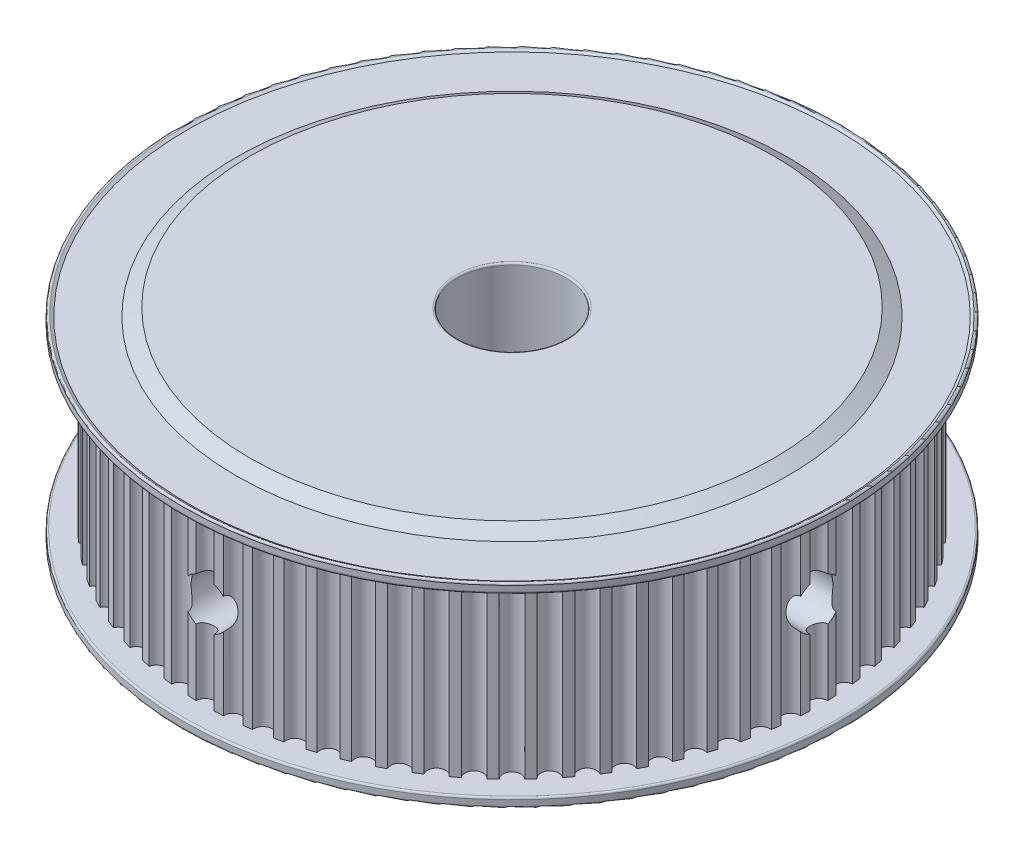
SolidWorks part; units mm, degrees
material "1060 Alloy"
ref_plane "Front Plane" through (0, 0, 0) normal (0, 0, 1) x (1, 0, 0)
ref_plane "Top Plane" through (0, 0, 0) normal (0, 1, 0) x (1, 0, 0)
ref_plane "Right Plane" through (0, 0, 0) normal (1, 0, 0) x (0, 0, -1)
sketch "Sketch1" plane through (0, 0, 0) normal (0, 0, 1) x (1, 0, 0)
  line L0 (0, 0) -> (0, 23) construction
  line L1 (0, 0) -> (0, 1.75)
  line L2 (0, 1.75) -> (36.5, 1.75)
  line L3 (36.5, 1.75) -> (36.5, 0.55)
  line L4 (36.5, 0.55) -> (35.8938, 0.9)
  line L5 (35.8938, 0.9) -> (30.5588, 0.9)
  line L6 (30.5588, 0.9) -> (29, 0)
  line L7 (29, 0) -> (0, 0)
  dimension "D1" = 23
  dimension "D3" = 36.5
  dimension "D4" = 29
  dimension "D5" = 150
  dimension "D6" = 150
  dimension "D7" = 1.75
  dimension "D8" = 1.2
  dimension "D9" = 0.85
revolve "Revolve1" add sketch "Sketch1" angle 360 about L0
fillet "Fillet1" radius 0.2 2 edges at (0, 0.55, -36.5) (0, 1.75, -36.5)
sketch "Sketch2" plane through (0, 1.75, 0) normal (0, 1, 0) x (1, 0, 0)
  arc A0 (1.9659, 33.9431) -> (0.9999, 33.9853) centre (0, 0) ccw
  circle A1 centre (0, 0) radius 33 construction
  arc A2 (-0.9999, 33.9853) -> (0.9999, 33.9853) centre (0, 34) ccw
  arc A3 (4.9168, 33.6426) -> (3.9581, 33.7688) centre (0, 0) ccw
  arc A4 (1.9659, 33.9431) -> (3.9581, 33.7688) centre (2.9633, 33.8706) ccw
  arc A5 (7.8302, 33.0861) -> (6.8862, 33.2954) centre (0, 0) ccw
  arc A6 (4.9168, 33.6426) -> (6.8862, 33.2954) centre (5.904, 33.4835) ccw
  arc A7 (10.6841, 32.2777) -> (9.7619, 32.5685) centre (0, 0) ccw
  arc A8 (7.8302, 33.0861) -> (9.7619, 32.5685) centre (8.7998, 32.8415) ccw
  arc A9 (13.4566, 31.2237) -> (12.5632, 31.5937) centre (0, 0) ccw
  arc A10 (10.6841, 32.2777) -> (12.5632, 31.5937) centre (11.6287, 31.9495) ccw
  arc A11 (16.1267, 29.9321) -> (15.269, 30.3786) centre (0, 0) ccw
  arc A12 (13.4566, 31.2237) -> (15.269, 30.3786) centre (14.369, 30.8145) ccw
  arc A13 (18.6741, 28.4126) -> (17.8586, 28.9322) centre (0, 0) ccw
  arc A14 (16.1267, 29.9321) -> (17.8586, 28.9322) centre (17, 29.4449) ccw
  arc A15 (21.0794, 26.677) -> (20.3122, 27.2656) centre (0, 0) ccw
  arc A16 (18.6741, 28.4126) -> (20.3122, 27.2656) centre (19.5016, 27.8512) ccw
  arc A17 (23.3242, 24.7383) -> (22.6113, 25.3915) centre (0, 0) ccw
  arc A18 (21.0794, 26.677) -> (22.6113, 25.3915) centre (21.8548, 26.0455) ccw
  arc A19 (25.3915, 22.6113) -> (24.7383, 23.3242) centre (0, 0) ccw
  arc A20 (23.3242, 24.7383) -> (24.7383, 23.3242) centre (24.0416, 24.0416) ccw
  arc A21 (27.2656, 20.3122) -> (26.677, 21.0794) centre (0, 0) ccw
  arc A22 (25.3915, 22.6113) -> (26.677, 21.0794) centre (26.0455, 21.8548) ccw
  arc A23 (28.9322, 17.8586) -> (28.4126, 18.6741) centre (0, 0) ccw
  arc A24 (27.2656, 20.3122) -> (28.4126, 18.6741) centre (27.8512, 19.5016) ccw
  arc A25 (30.3786, 15.269) -> (29.9321, 16.1267) centre (0, 0) ccw
  arc A26 (28.9322, 17.8586) -> (29.9321, 16.1267) centre (29.4449, 17) ccw
  arc A27 (31.5937, 12.5632) -> (31.2237, 13.4566) centre (0, 0) ccw
  arc A28 (30.3786, 15.269) -> (31.2237, 13.4566) centre (30.8145, 14.369) ccw
  arc A29 (32.5685, 9.7619) -> (32.2777, 10.6841) centre (0, 0) ccw
  arc A30 (31.5937, 12.5632) -> (32.2777, 10.6841) centre (31.9495, 11.6287) ccw
  arc A31 (33.2954, 6.8862) -> (33.0861, 7.8302) centre (0, 0) ccw
  arc A32 (32.5685, 9.7619) -> (33.0861, 7.8302) centre (32.8415, 8.7998) ccw
  arc A33 (33.7688, 3.9581) -> (33.6426, 4.9168) centre (0, 0) ccw
  arc A34 (33.2954, 6.8862) -> (33.6426, 4.9168) centre (33.4835, 5.904) ccw
  arc A35 (33.9853, 0.9999) -> (33.9431, 1.9659) centre (0, 0) ccw
  arc A36 (33.7688, 3.9581) -> (33.9431, 1.9659) centre (33.8706, 2.9633) ccw
  arc A37 (33.9431, -1.9659) -> (33.9853, -0.9999) centre (0, 0) ccw
  arc A38 (33.9853, 0.9999) -> (33.9853, -0.9999) centre (34, 0) ccw
  arc A39 (33.6426, -4.9168) -> (33.7688, -3.9581) centre (0, 0) ccw
  arc A40 (33.9431, -1.9659) -> (33.7688, -3.9581) centre (33.8706, -2.9633) ccw
  arc A41 (33.0861, -7.8302) -> (33.2954, -6.8862) centre (0, 0) ccw
  arc A42 (33.6426, -4.9168) -> (33.2954, -6.8862) centre (33.4835, -5.904) ccw
  arc A43 (32.2777, -10.6841) -> (32.5685, -9.7619) centre (0, 0) ccw
  arc A44 (33.0861, -7.8302) -> (32.5685, -9.7619) centre (32.8415, -8.7998) ccw
  arc A45 (31.2237, -13.4566) -> (31.5937, -12.5632) centre (0, 0) ccw
  arc A46 (32.2777, -10.6841) -> (31.5937, -12.5632) centre (31.9495, -11.6287) ccw
  arc A47 (29.9321, -16.1267) -> (30.3786, -15.269) centre (0, 0) ccw
  arc A48 (31.2237, -13.4566) -> (30.3786, -15.269) centre (30.8145, -14.369) ccw
  arc A49 (28.4126, -18.6741) -> (28.9322, -17.8586) centre (0, 0) ccw
  arc A50 (29.9321, -16.1267) -> (28.9322, -17.8586) centre (29.4449, -17) ccw
  arc A51 (26.677, -21.0794) -> (27.2656, -20.3122) centre (0, 0) ccw
  arc A52 (28.4126, -18.6741) -> (27.2656, -20.3122) centre (27.8512, -19.5016) ccw
  arc A53 (24.7383, -23.3242) -> (25.3915, -22.6113) centre (0, 0) ccw
  arc A54 (26.677, -21.0794) -> (25.3915, -22.6113) centre (26.0455, -21.8548) ccw
  arc A55 (22.6113, -25.3915) -> (23.3242, -24.7383) centre (0, 0) ccw
  arc A56 (24.7383, -23.3242) -> (23.3242, -24.7383) centre (24.0416, -24.0416) ccw
  arc A57 (20.3122, -27.2656) -> (21.0794, -26.677) centre (0, 0) ccw
  arc A58 (22.6113, -25.3915) -> (21.0794, -26.677) centre (21.8548, -26.0455) ccw
  arc A59 (17.8586, -28.9322) -> (18.6741, -28.4126) centre (0, 0) ccw
  arc A60 (20.3122, -27.2656) -> (18.6741, -28.4126) centre (19.5016, -27.8512) ccw
  arc A61 (15.269, -30.3786) -> (16.1267, -29.9321) centre (0, 0) ccw
  arc A62 (17.8586, -28.9322) -> (16.1267, -29.9321) centre (17, -29.4449) ccw
  arc A63 (12.5632, -31.5937) -> (13.4566, -31.2237) centre (0, 0) ccw
  arc A64 (15.269, -30.3786) -> (13.4566, -31.2237) centre (14.369, -30.8145) ccw
  arc A65 (9.7619, -32.5685) -> (10.6841, -32.2777) centre (0, 0) ccw
  arc A66 (12.5632, -31.5937) -> (10.6841, -32.2777) centre (11.6287, -31.9495) ccw
  arc A67 (6.8862, -33.2954) -> (7.8302, -33.0861) centre (0, 0) ccw
  arc A68 (9.7619, -32.5685) -> (7.8302, -33.0861) centre (8.7998, -32.8415) ccw
  arc A69 (3.9581, -33.7688) -> (4.9168, -33.6426) centre (0, 0) ccw
  arc A70 (6.8862, -33.2954) -> (4.9168, -33.6426) centre (5.904, -33.4835) ccw
  arc A71 (0.9999, -33.9853) -> (1.9659, -33.9431) centre (0, 0) ccw
  arc A72 (3.9581, -33.7688) -> (1.9659, -33.9431) centre (2.9633, -33.8706) ccw
  arc A73 (-1.9659, -33.9431) -> (-0.9999, -33.9853) centre (0, 0) ccw
  arc A74 (0.9999, -33.9853) -> (-0.9999, -33.9853) centre (0, -34) ccw
  arc A75 (-4.9168, -33.6426) -> (-3.9581, -33.7688) centre (0, 0) ccw
  arc A76 (-1.9659, -33.9431) -> (-3.9581, -33.7688) centre (-2.9633, -33.8706) ccw
  arc A77 (-7.8302, -33.0861) -> (-6.8862, -33.2954) centre (0, 0) ccw
  arc A78 (-4.9168, -33.6426) -> (-6.8862, -33.2954) centre (-5.904, -33.4835) ccw
  arc A79 (-10.6841, -32.2777) -> (-9.7619, -32.5685) centre (0, 0) ccw
  arc A80 (-7.8302, -33.0861) -> (-9.7619, -32.5685) centre (-8.7998, -32.8415) ccw
  arc A81 (-13.4566, -31.2237) -> (-12.5632, -31.5937) centre (0, 0) ccw
  arc A82 (-10.6841, -32.2777) -> (-12.5632, -31.5937) centre (-11.6287, -31.9495) ccw
  arc A83 (-16.1267, -29.9321) -> (-15.269, -30.3786) centre (0, 0) ccw
  arc A84 (-13.4566, -31.2237) -> (-15.269, -30.3786) centre (-14.369, -30.8145) ccw
  arc A85 (-18.6741, -28.4126) -> (-17.8586, -28.9322) centre (0, 0) ccw
  arc A86 (-16.1267, -29.9321) -> (-17.8586, -28.9322) centre (-17, -29.4449) ccw
  arc A87 (-21.0794, -26.677) -> (-20.3122, -27.2656) centre (0, 0) ccw
  arc A88 (-18.6741, -28.4126) -> (-20.3122, -27.2656) centre (-19.5016, -27.8512) ccw
  arc A89 (-23.3242, -24.7383) -> (-22.6113, -25.3915) centre (0, 0) ccw
  arc A90 (-21.0794, -26.677) -> (-22.6113, -25.3915) centre (-21.8548, -26.0455) ccw
  arc A91 (-25.3915, -22.6113) -> (-24.7383, -23.3242) centre (0, 0) ccw
  arc A92 (-23.3242, -24.7383) -> (-24.7383, -23.3242) centre (-24.0416, -24.0416) ccw
  arc A93 (-27.2656, -20.3122) -> (-26.677, -21.0794) centre (0, 0) ccw
  arc A94 (-25.3915, -22.6113) -> (-26.677, -21.0794) centre (-26.0455, -21.8548) ccw
  arc A95 (-28.9322, -17.8586) -> (-28.4126, -18.6741) centre (0, 0) ccw
  arc A96 (-27.2656, -20.3122) -> (-28.4126, -18.6741) centre (-27.8512, -19.5016) ccw
  arc A97 (-30.3786, -15.269) -> (-29.9321, -16.1267) centre (0, 0) ccw
  arc A98 (-28.9322, -17.8586) -> (-29.9321, -16.1267) centre (-29.4449, -17) ccw
  arc A99 (-31.5937, -12.5632) -> (-31.2237, -13.4566) centre (0, 0) ccw
  arc A100 (-30.3786, -15.269) -> (-31.2237, -13.4566) centre (-30.8145, -14.369) ccw
  arc A101 (-32.5685, -9.7619) -> (-32.2777, -10.6841) centre (0, 0) ccw
  arc A102 (-31.5937, -12.5632) -> (-32.2777, -10.6841) centre (-31.9495, -11.6287) ccw
  arc A103 (-33.2954, -6.8862) -> (-33.0861, -7.8302) centre (0, 0) ccw
  arc A104 (-32.5685, -9.7619) -> (-33.0861, -7.8302) centre (-32.8415, -8.7998) ccw
  arc A105 (-33.7688, -3.9581) -> (-33.6426, -4.9168) centre (0, 0) ccw
  arc A106 (-33.2954, -6.8862) -> (-33.6426, -4.9168) centre (-33.4835, -5.904) ccw
  arc A107 (-33.9853, -0.9999) -> (-33.9431, -1.9659) centre (0, 0) ccw
  arc A108 (-33.7688, -3.9581) -> (-33.9431, -1.9659) centre (-33.8706, -2.9633) ccw
  arc A109 (-33.9431, 1.9659) -> (-33.9853, 0.9999) centre (0, 0) ccw
  arc A110 (-33.9853, -0.9999) -> (-33.9853, 0.9999) centre (-34, 0) ccw
  arc A111 (-33.6426, 4.9168) -> (-33.7688, 3.9581) centre (0, 0) ccw
  arc A112 (-33.9431, 1.9659) -> (-33.7688, 3.9581) centre (-33.8706, 2.9633) ccw
  arc A113 (-33.0861, 7.8302) -> (-33.2954, 6.8862) centre (0, 0) ccw
  arc A114 (-33.6426, 4.9168) -> (-33.2954, 6.8862) centre (-33.4835, 5.904) ccw
  arc A115 (-32.2777, 10.6841) -> (-32.5685, 9.7619) centre (0, 0) ccw
  arc A116 (-33.0861, 7.8302) -> (-32.5685, 9.7619) centre (-32.8415, 8.7998) ccw
  arc A117 (-31.2237, 13.4566) -> (-31.5937, 12.5632) centre (0, 0) ccw
  arc A118 (-32.2777, 10.6841) -> (-31.5937, 12.5632) centre (-31.9495, 11.6287) ccw
  arc A119 (-29.9321, 16.1267) -> (-30.3786, 15.269) centre (0, 0) ccw
  arc A120 (-31.2237, 13.4566) -> (-30.3786, 15.269) centre (-30.8145, 14.369) ccw
  arc A121 (-28.4126, 18.6741) -> (-28.9322, 17.8586) centre (0, 0) ccw
  arc A122 (-29.9321, 16.1267) -> (-28.9322, 17.8586) centre (-29.4449, 17) ccw
  arc A123 (-26.677, 21.0794) -> (-27.2656, 20.3122) centre (0, 0) ccw
  arc A124 (-28.4126, 18.6741) -> (-27.2656, 20.3122) centre (-27.8512, 19.5016) ccw
  arc A125 (-24.7383, 23.3242) -> (-25.3915, 22.6113) centre (0, 0) ccw
  arc A126 (-26.677, 21.0794) -> (-25.3915, 22.6113) centre (-26.0455, 21.8548) ccw
  arc A127 (-22.6113, 25.3915) -> (-23.3242, 24.7383) centre (0, 0) ccw
  arc A128 (-24.7383, 23.3242) -> (-23.3242, 24.7383) centre (-24.0416, 24.0416) ccw
  arc A129 (-20.3122, 27.2656) -> (-21.0794, 26.677) centre (0, 0) ccw
  arc A130 (-22.6113, 25.3915) -> (-21.0794, 26.677) centre (-21.8548, 26.0455) ccw
  arc A131 (-17.8586, 28.9322) -> (-18.6741, 28.4126) centre (0, 0) ccw
  arc A132 (-20.3122, 27.2656) -> (-18.6741, 28.4126) centre (-19.5016, 27.8512) ccw
  arc A133 (-15.269, 30.3786) -> (-16.1267, 29.9321) centre (0, 0) ccw
  arc A134 (-17.8586, 28.9322) -> (-16.1267, 29.9321) centre (-17, 29.4449) ccw
  arc A135 (-12.5632, 31.5937) -> (-13.4566, 31.2237) centre (0, 0) ccw
  arc A136 (-15.269, 30.3786) -> (-13.4566, 31.2237) centre (-14.369, 30.8145) ccw
  arc A137 (-9.7619, 32.5685) -> (-10.6841, 32.2777) centre (0, 0) ccw
  arc A138 (-12.5632, 31.5937) -> (-10.6841, 32.2777) centre (-11.6287, 31.9495) ccw
  arc A139 (-6.8862, 33.2954) -> (-7.8302, 33.0861) centre (0, 0) ccw
  arc A140 (-9.7619, 32.5685) -> (-7.8302, 33.0861) centre (-8.7998, 32.8415) ccw
  arc A141 (-3.9581, 33.7688) -> (-4.9168, 33.6426) centre (0, 0) ccw
  arc A142 (-6.8862, 33.2954) -> (-4.9168, 33.6426) centre (-5.904, 33.4835) ccw
  arc A143 (-0.9999, 33.9853) -> (-1.9659, 33.9431) centre (0, 0) ccw
  arc A144 (-3.9581, 33.7688) -> (-1.9659, 33.9431) centre (-2.9633, 33.8706) ccw
  dimension "D1" = 68
  dimension "D2" = 66
  dimension "D3" = 72
extrude "Boss-Extrude1" add sketch "Sketch2" along normal blind 19.5
ref_plane "Plane1" through (0, 11.5, 0) normal (0, 1, 0) x (1, 0, 0)
mirror "Mirror1" about plane through (0, 11.5, 0) normal (0, 1, 0) of "Fillet1", "Revolve1"
sketch "Sketch4" plane through (0, 0, 0) normal (0, 0, 1) x (1, 0, 0)
  line L0 (-0.9999, 21.25) -> (-0.9999, 1.75) construction
  circle A0 centre (0, 11.5) radius 2.6
  point P5 (-0.9999, 11.5)
  dimension "D1" = 5.2
extrude "Cut-Extrude1" cut sketch "Sketch4" along normal blind 36.5
sketch "Sketch5" plane through (0, 0, 0) normal (1, 0, 0) x (0, 0, -1)
  line L1 (-0.9999, 21.25) -> (-0.9999, 1.75) construction
  circle A0 centre (0, 11.5) radius 2.6
  point P5 (-0.9999, 11.5)
  dimension "D1" = 5.2
extrude "Cut-Extrude2" cut sketch "Sketch5" along normal blind 36.5
sketch "Sketch3" plane through (0, 23, 0) normal (0, 1, 0) x (1, 0, 0)
  circle A0 centre (0, 0) radius 6
  dimension "D1" = 12
extrude "Cut-Extrude3" cut sketch "Sketch3" against normal through all
fillet "Fillet2" radius 0.2 2 edges at (0, 0, 6) (0, 23, 6)
scale "Scale1" scale about centroid uniform scaling yes scale factor 0.5
